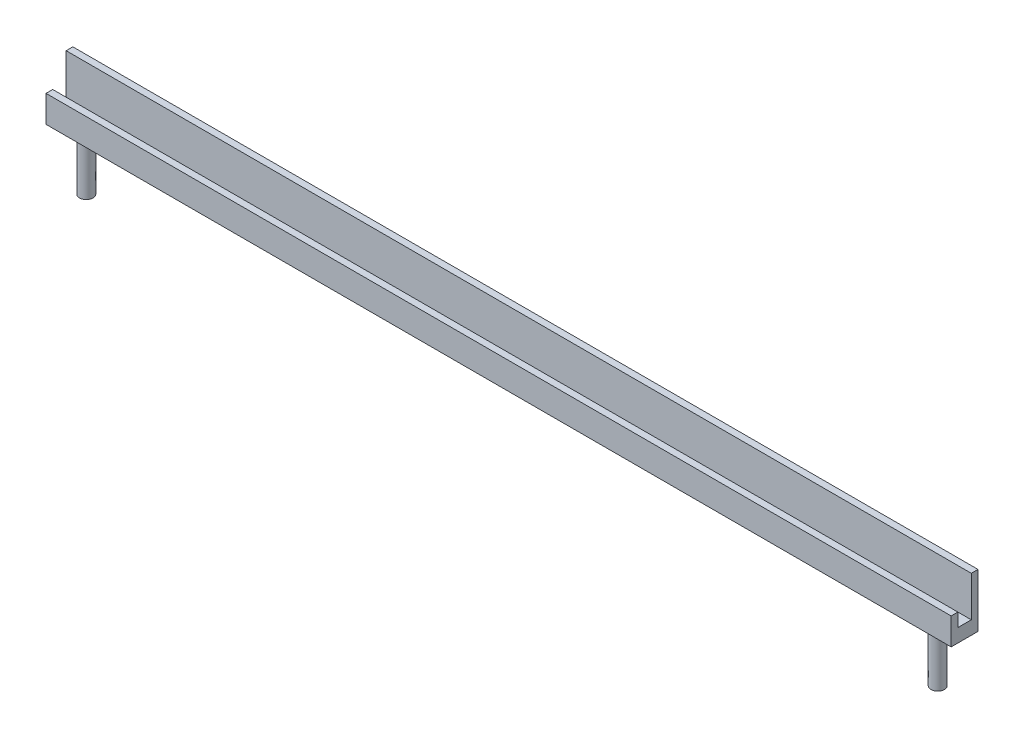
SolidWorks part; units mm, degrees
ref_plane "Front Plane" through (0, 0, 0) normal (0, 0, 1) x (1, 0, 0)
ref_plane "Top Plane" through (0, 0, 0) normal (0, 1, 0) x (1, 0, 0)
ref_plane "Right Plane" through (0, 0, 0) normal (1, 0, 0) x (0, 0, -1)
sketch "Sketch1" plane through (0, 0, 0) normal (0, 1, 0) x (1, 0, 0)
  line L1 (-168.5, 5) -> (168.5, 5)
  line L2 (-168.5, 5) -> (-168.5, -5)
  line L3 (-168.5, -5) -> (168.5, -5)
  line L4 (168.5, 5) -> (168.5, -5)
  line L5 (-168.5, 5) -> (168.5, -5) construction
  line L6 (-168.5, -5) -> (168.5, 5) construction
  point P0 (0, 0)
  dimension "D1" = 337
  dimension "D2" = 10
extrude "Boss-Extrude1" add sketch "Sketch1" along normal blind 5
sketch "Sketch2" plane through (0, 5, 0) normal (0, 1, 0) x (1, 0, 0)
  line L0 (168.5, -5) -> (168.5, 5) construction
  line L1 (168.5, -2.5) -> (-168.5, -2.5)
  line L2 (168.5, -2.5) -> (168.5, -5)
  line L3 (168.5, -5) -> (-168.5, -5)
  line L4 (-168.5, -2.5) -> (-168.5, -5)
  dimension "D1" = 2.5
extrude "Boss-Extrude2" add sketch "Sketch2" along normal blind 5
sketch "Sketch3" plane through (0, 5, 0) normal (0, 1, 0) x (1, 0, 0)
  line L0 (-168.5, 5) -> (-168.5, -2.5) construction
  line L1 (-168.5, 2.5) -> (168.5, 2.5)
  line L2 (-168.5, 2.5) -> (-168.5, 5)
  line L3 (-168.5, 5) -> (168.5, 5)
  line L4 (168.5, 2.5) -> (168.5, 5)
  dimension "D1" = 2.5
extrude "Boss-Extrude3" add sketch "Sketch3" along normal blind 15
sketch "Sketch4" plane through (0, 0, 0) normal (0, -1, 0) x (1, 0, 0)
  line L0 (-168.5, -5) -> (-168.5, 5) construction
  line L1 (168.5, 5) -> (168.5, -5) construction
  circle A0 centre (-158.5, 0) radius 2.5
  circle A1 centre (158.5, 0) radius 2.5
  point P5 (-168.5, 0)
  point P8 (168.5, 0)
  dimension "D2" = 5
  dimension "D4" = 5
  dimension "D1" = 10
  dimension "D3" = 10
extrude "Boss-Extrude4" add sketch "Sketch4" along normal blind 20
